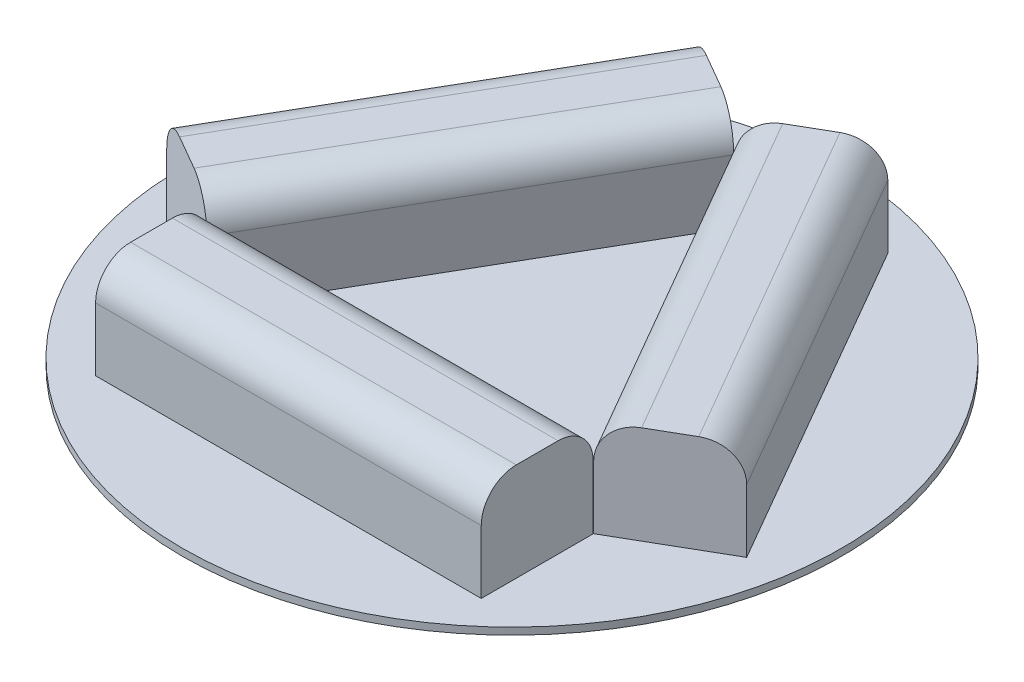
SolidWorks part; units mm, degrees
ref_plane "Front Plane" through (0, 0, 0) normal (0, 0, 1) x (1, 0, 0)
ref_plane "Top Plane" through (0, 0, 0) normal (0, 1, 0) x (1, 0, 0)
ref_plane "Right Plane" through (0, 0, 0) normal (1, 0, 0) x (0, 0, -1)
sketch "Sketch1" plane through (0, 0, 0) normal (0, 1, 0) x (1, 0, 0)
  line L3 (0.0237, 0.0137) -> (13.8564, 8)
  line L4 (27.5, -47.6715) -> (27.5, -63.6314)
  line L5 (27.5237, -47.6177) -> (41.3564, -39.6314)
  line L6 (-27.5, -47.6715) -> (-27.5, -63.6314)
  line L7 (-27.5, -63.6314) -> (27.5, -63.6314)
  line L8 (41.3564, -39.6314) -> (13.8564, 8)
  line L9 (-27.7891, -47.4645) -> (-41.3564, -39.6314)
  line L10 (-0.2891, 0.1669) -> (-13.8564, 8)
  line L11 (-41.3564, -39.6314) -> (-13.8564, 8)
  line L12 (-0.2891, 0.1669) -> (-27.7891, -47.4645)
  line L13 (-27.5, -47.6715) -> (27.5, -47.6715)
  line L14 (27.5237, -47.6177) -> (0.0237, 0.0137)
extrude "Boss-Extrude1" add sketch "Sketch1" along normal blind 15
fillet "Fillet1" radius 5 1 edges at (0, 15, 63.6314)
fillet "Fillet2" radius 5 1 edges at (0, 15, 47.6715)
fillet "Fillet3" radius 5 1 edges at (27.6064, 15, 15.8157)
fillet "Fillet4" radius 5 1 edges at (13.7737, 15, 23.802)
fillet "Fillet5" radius 5 1 edges at (-14.0391, 15, 23.6488)
fillet "Fillet6" radius 5 1 edges at (-27.6064, 15, 15.8157)
shell "Shell1" thickness 1
shell "Shell2" thickness 1
shell "Shell3" thickness 1
fillet "Fillet7" radius 3 5 edges at (-28.1551, 5, 46.0985) (-38.9758, 12.8284, 39.8512) (-39.9904, 5, 39.2654) (-29.1697, 12.8284, 45.5127) (-34.0728, 14, 42.6819)
fillet "Fillet8" radius 3 5 edges at (-12.4758, 12.8284, -6.0482) (-2.6697, 12.8284, -0.3867) (-1.6551, 5, 0.1991) (-13.4904, 5, -6.634) (-7.5728, 14, -3.2174)
fillet "Fillet9" radius 3 5 edges at (2.4043, 12.8284, -0.2334) (12.4758, 12.8284, -6.0482) (13.4904, 5, -6.634) (1.3897, 5, 0.3523) (7.4401, 14, -3.1408)
fillet "Fillet10" radius 3 5 edges at (-26.5, 5, 62.6314) (-26.5, 12.8284, 49.8431) (-26.5, 5, 48.6715) (-26.5, 12.8284, 61.4598) (-26.5, 14, 55.6515)
fillet "Fillet11" radius 3 5 edges at (26.5, 12.8284, 49.8431) (26.5, 12.8284, 61.4598) (26.5, 5, 62.6314) (26.5, 5, 48.6715) (26.5, 14, 55.6515)
fillet "Fillet12" radius 3 5 edges at (39.9904, 5, 39.2654) (28.9043, 12.8284, 45.6659) (27.8897, 5, 46.2517) (38.9758, 12.8284, 39.8512) (33.9401, 14, 42.7585)
sketch "Sketch2" plane through (0, 0, 0) normal (0, 1, 0) x (1, 0, 0)
  line L0 (0, 0) -> (0, -47.6715) construction
  line L1 (-27.5, -47.6715) -> (27.5, -47.6715) construction
  line L2 (27.5237, -47.6177) -> (-14.0391, -23.6488) construction
  line L3 (-0.2891, 0.1669) -> (-27.7891, -47.4645) construction
  line L4 (-27.5, -47.6715) -> (13.7737, -23.802) construction
  line L5 (27.5237, -47.6177) -> (0.0237, 0.0137) construction
  circle A0 centre (0, -31.745) radius 47
  dimension "D1" = 94
extrude "Boss-Extrude2" add sketch "Sketch2" along normal blind 1
sketch "Sketch3" plane through (0, 0, 0) normal (0, 1, 0) x (1, 0, 0)
  line L0 (-34.0728, -42.6819) -> (-7.5728, 3.2174) construction
  line L1 (-36.5263, -41.2654) -> (-31.6192, -44.0985) construction
  line L2 (-5.1192, 1.8009) -> (-10.0263, 4.634) construction
  line L3 (7.4401, 3.1408) -> (32.4401, -40.1605) construction
  line L4 (10.0263, 4.634) -> (4.8538, 1.6477) construction
  line L5 (35.0263, -38.6673) -> (29.8538, -41.6536) construction
  line L6 (-26.5, -55.6515) -> (26.5, -55.6515) construction
  line L7 (-26.5, -52.6715) -> (-26.5, -58.6314) construction
  line L8 (26.5, -58.6314) -> (26.5, -52.6715) construction
  line L9 (3.987, 1.1412) -> (10.8863, 5.1365)
  line L10 (-23.5, -48.6715) -> (23.5, -48.6715)
  line L11 (-26.5, -51.6715) -> (-26.5, -59.6314)
  line L12 (-23.5, -62.6314) -> (23.5, -62.6314)
  line L13 (26.5, -51.6715) -> (26.5, -59.6314)
  line L14 (-26.5, -48.6715) -> (26.5, -62.6314) construction
  line L15 (-26.5, -62.6314) -> (26.5, -48.6715) construction
  line L16 (37.1913, -34.4173) -> (14.9878, 4.0404)
  line L17 (29.1888, -42.5017) -> (36.0933, -38.5154)
  line L20 (2.8923, -2.9549) -> (25.0907, -41.4036)
  line L22 (-26.6551, -43.5004) -> (-3.1551, -2.7972)
  line L24 (-38.4904, -36.6673) -> (-14.9904, 4.0359)
  line L26 (-10.8923, 5.134) -> (-4.2532, 1.3009)
  line L27 (-37.3923, -40.7654) -> (-30.7532, -44.5985)
  arc A0 (37.1913, -34.4173) -> (36.0933, -38.5154) centre (34.5933, -35.9173) cw
  arc A1 (25.0907, -41.4036) -> (29.1888, -42.5017) centre (27.6888, -39.9036) ccw
  arc A2 (-23.5, -48.6715) -> (-26.5, -51.6715) centre (-23.5, -51.6715) ccw
  arc A3 (-26.5, -59.6314) -> (-23.5, -62.6314) centre (-23.5, -59.6314) ccw
  arc A4 (23.5, -62.6314) -> (26.5, -59.6314) centre (23.5, -59.6314) ccw
  arc A5 (23.5, -48.6715) -> (26.5, -51.6715) centre (23.5, -51.6715) cw
  arc A6 (-38.4904, -36.6673) -> (-37.3923, -40.7654) centre (-35.8923, -38.1673) ccw
  arc A7 (-30.7532, -44.5985) -> (-26.6551, -43.5004) centre (-29.2532, -42.0004) ccw
  arc A8 (-10.8923, 5.134) -> (-14.9904, 4.0359) centre (-12.3923, 2.5359) ccw
  arc A9 (-4.2532, 1.3009) -> (-3.1551, -2.7972) centre (-5.7532, -1.2972) cw
  arc A10 (10.8863, 5.1365) -> (14.9878, 4.0404) centre (12.3897, 2.5404) cw
  arc A11 (2.8923, -2.9549) -> (3.987, 1.1412) centre (5.4904, -1.4549) cw
  point P18 (0, -55.6515)
  point P32 (33.9401, -42.7585)
  point P33 (7.4401, 3.1408)
  point P37 (13.9915, -22.1793)
  point P40 (-14.9051, -23.1488)
  point P43 (-26.7404, -16.3157)
  point P46 (-7.5728, 3.2174)
  point P51 (-34.0728, -42.6819)
  dimension "D1" = 3
  dimension "D2" = 3
extrude "Cut-Extrude1" cut sketch "Sketch3" along normal blind 1 and the other way blind 13
